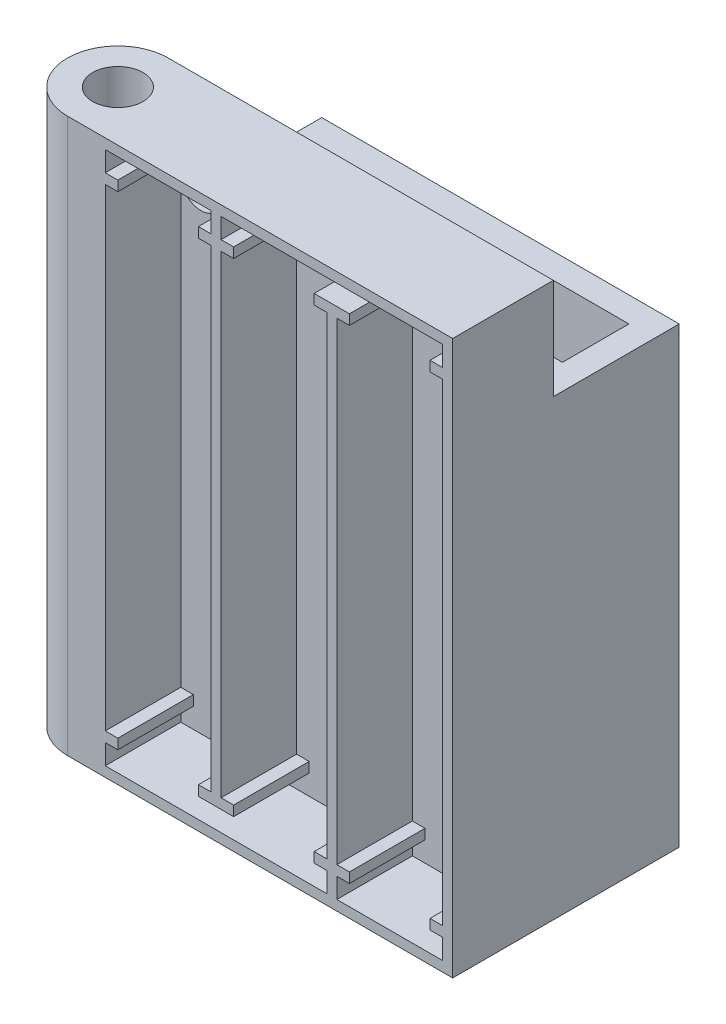
SolidWorks part; units mm, degrees
ref_plane "Front Plane" through (0, 0, 0) normal (0, 0, 1) x (1, 0, 0)
ref_plane "Top Plane" through (0, 0, 0) normal (0, 1, 0) x (1, 0, 0)
ref_plane "Right Plane" through (0, 0, 0) normal (1, 0, 0) x (0, 0, -1)
sketch "Sketch1" plane through (0, 0, 0) normal (0, 1, 0) x (1, 0, 0)
  line L1 (-15.25, -5) -> (15.25, -5)
  line L2 (-15.25, -5) -> (-15.25, 5)
  line L3 (-15.25, 5) -> (15.25, 5)
  line L4 (15.25, -5) -> (15.25, 5)
  line L5 (-15.25, -5) -> (15.25, 5) construction
  line L6 (-15.25, 5) -> (15.25, -5) construction
  point P0 (0, 0)
  dimension "D1" = 30.5
  dimension "D2" = 10
extrude "Boss-Extrude1" add sketch "Sketch1" along normal blind 2.5
sketch "Sketch2" plane through (0, 0, 0) normal (0, 1, 0) x (1, 0, 0)
  line L0 (15.25, 5) -> (-15.25, 5) construction
  line L1 (-17.75, -7.5) -> (17.75, -7.5)
  line L2 (-17.75, -7.5) -> (-17.75, 7.5)
  line L3 (-17.75, 7.5) -> (17.75, 7.5)
  line L4 (17.75, -7.5) -> (17.75, 7.5)
  line L5 (-17.75, -7.5) -> (17.75, 7.5) construction
  line L6 (-17.75, 7.5) -> (17.75, -7.5) construction
  line L7 (-15.25, 5) -> (-15.25, -5) construction
  line L8 (-15.25, 5) -> (-15.25, -5)
  line L9 (-15.25, -5) -> (-10.25, -5)
  line L10 (-15.25, -5) -> (15.25, -5) construction
  line L11 (-10.25, -5) -> (-10.25, -1.6)
  line L12 (-10.25, -1.6) -> (15.25, -1.6)
  line L13 (15.25, -5) -> (15.25, 5) construction
  line L14 (15.25, -1.6) -> (15.25, 5)
  line L15 (15.25, 5) -> (-15.25, 5)
  point P0 (0, 0)
  dimension "D1" = 2.5
  dimension "D2" = 2.5
  dimension "D3" = 6.6
  dimension "D4" = 5
extrude "Boss-Extrude3" add sketch "Sketch2" along normal blind 45
sketch "Sketch3" plane through (0, 45, 0) normal (0, 1, 0) x (1, 0, 0)
  line L0 (-10.25, -5) -> (-2.75, -5)
  line L1 (-2.75, -5) -> (-2.75, -1.6)
  line L2 (-10.25, -1.6) -> (15.25, -1.6) construction
  line L3 (-2.75, -1.6) -> (-10.25, -1.6)
  line L4 (-10.25, -1.6) -> (-10.25, -5)
  dimension "D1" = 7.5
extrude "Cut-Extrude1" cut sketch "Sketch3" against normal blind 29
sketch "Sketch4" plane through (0, 45, 0) normal (0, 1, 0) x (1, 0, 0)
  line L0 (-15.25, -5) -> (-17.75, -5) construction
  line L1 (-17.75, 7.5) -> (-17.75, -7.5) construction
  line L3 (17.75, -7.5) -> (-17.75, -7.5)
  line L4 (17.75, -7.5) -> (17.75, -5)
  line L5 (17.75, -5) -> (-17.75, -5)
  line L6 (-17.75, -7.5) -> (-17.75, -5)
extrude "Boss-Extrude4" add sketch "Sketch4" along normal blind 10
sketch "Sketch5" plane through (0, 0, 7.5) normal (0, 0, 1) x (1, 0, 0)
  line L5 (-17.75, 27.5) -> (17.75, 27.5) construction
  line L11 (-17.75, 55) -> (-17.75, 0) construction
  line L20 (17.75, 55) -> (17.75, 0) construction
  line L21 (-17.75, 0) -> (-17.75, 55)
  line L22 (-17.75, 55) -> (17.75, 55)
  line L23 (17.75, 55) -> (17.75, 0)
  line L24 (-16.75, 1) -> (-16.75, 54)
  line L25 (-16.75, 54) -> (16.75, 54)
  line L26 (16.75, 54) -> (16.75, 1)
  line L27 (-17.75, 0) -> (17.75, 0)
  line L28 (-16.75, 1) -> (16.75, 1)
  point P16 (16.75, 27.5)
  point P17 (-16.75, 27.5)
  dimension "D1" = 1
  dimension "D2" = 1
  dimension "D3" = 1
extrude "Boss-Extrude5" add sketch "Sketch5" along normal blind 7.5
sketch "Sketch6" plane through (0, 0, 7.5) normal (0, 0, 1) x (1, 0, 0)
  line L0 (-6.25, 54) -> (-6.25, 52)
  line L1 (16.75, 54) -> (-16.75, 54) construction
  line L2 (-16.75, 1) -> (16.75, 1) construction
  line L3 (-6.25, 1) -> (-5.25, 1)
  line L4 (-5.25, 1) -> (-5.25, 3)
  line L5 (-5.25, 54) -> (-6.25, 54)
  line L6 (-16.75, 54) -> (-16.75, 1) construction
  line L7 (6.25, 54) -> (5.25, 54)
  line L8 (5.25, 54) -> (5.25, 52)
  line L9 (5.25, 1) -> (6.25, 1)
  line L10 (6.25, 1) -> (6.25, 3)
  line L13 (16.75, 1) -> (16.75, 54) construction
  line L14 (-16.75, 52) -> (-6.25, 52)
  line L15 (-16.75, 52) -> (-16.75, 51)
  line L16 (-16.75, 51) -> (-6.25, 51)
  line L17 (16.75, 52) -> (16.75, 51)
  line L18 (16.75, 54) -> (-16.75, 54) construction
  line L19 (-16.75, 27.5) -> (16.75, 27.5) construction
  line L20 (-16.75, 54) -> (-16.75, 1) construction
  line L21 (-16.75, 4) -> (-6.25, 4)
  line L22 (16.75, 3) -> (16.75, 4)
  line L23 (-16.75, 3) -> (-6.25, 3)
  line L24 (-16.75, 3) -> (-16.75, 4)
  line L25 (-6.25, 51) -> (-6.25, 4)
  line L26 (-5.25, 52) -> (-5.25, 54)
  line L27 (-5.25, 52) -> (5.25, 52)
  line L28 (-5.25, 51) -> (5.25, 51)
  line L29 (6.25, 52) -> (6.25, 54)
  line L30 (5.25, 51) -> (5.25, 4)
  line L31 (6.25, 52) -> (16.75, 52)
  line L32 (6.25, 51) -> (16.75, 51)
  line L33 (-5.25, 3) -> (5.25, 3)
  line L34 (-5.25, 4) -> (5.25, 4)
  line L35 (-6.25, 3) -> (-6.25, 1)
  line L36 (-5.25, 4) -> (-5.25, 51)
  line L37 (6.25, 3) -> (16.75, 3)
  line L38 (6.25, 4) -> (16.75, 4)
  line L39 (5.25, 3) -> (5.25, 1)
  line L40 (6.25, 4) -> (6.25, 51)
  dimension "D1" = 1
  dimension "D2" = 10.5
  dimension "D4" = 10.5
  dimension "D5" = 1
  dimension "D6" = 2
  dimension "D3" = 2
extrude "Boss-Extrude6" add sketch "Sketch6" along normal blind 7.5
sketch "Sketch7" plane through (0, 0, 15) normal (0, 0, 1) x (1, 0, 0)
  line L0 (-16.75, 27.5) -> (16.75, 27.5) construction
  line L1 (-16.75, 51) -> (-16.75, 4) construction
  line L2 (16.75, 4) -> (16.75, 51) construction
  line L3 (-11.5, 52) -> (-11.5, 51) construction
  line L6 (-6.25, 52) -> (-16.75, 52) construction
  line L9 (-16.75, 51) -> (-6.25, 51) construction
  line L12 (-4, 51) -> (-4, 52)
  line L13 (-15.5, 51) -> (-7.5, 51)
  line L14 (-15.5, 51) -> (-15.5, 52)
  line L15 (-15.5, 52) -> (-7.5, 52)
  line L16 (-7.5, 51) -> (-7.5, 52)
  line L17 (-15.5, 51) -> (-7.5, 52) construction
  line L18 (-15.5, 52) -> (-7.5, 51) construction
  line L19 (-4, 51) -> (4, 51)
  line L20 (4, 51) -> (4, 52)
  line L21 (-4, 52) -> (4, 52)
  line L22 (7.5, 51) -> (7.5, 52)
  line L23 (7.5, 51) -> (15.5, 51)
  line L24 (15.5, 51) -> (15.5, 52)
  line L25 (7.5, 52) -> (15.5, 52)
  line L28 (7.5, 4) -> (15.5, 4)
  line L29 (5.25, 54) -> (6.25, 54)
  line L30 (5.25, 54) -> (5.25, 52)
  line L31 (5.25, 52) -> (6.25, 52)
  line L32 (6.25, 54) -> (6.25, 52)
  line L33 (15.5, 4) -> (15.5, 3)
  line L34 (7.5, 3) -> (15.5, 3)
  line L35 (7.5, 4) -> (7.5, 3)
  line L36 (-4, 4) -> (4, 4)
  line L37 (4, 4) -> (4, 3)
  line L38 (-4, 3) -> (4, 3)
  line L39 (-4, 4) -> (-4, 3)
  line L40 (-15.5, 3) -> (-7.5, 3)
  line L41 (-7.5, 4) -> (-7.5, 3)
  line L42 (-15.5, 4) -> (-7.5, 4)
  line L43 (-15.5, 4) -> (-15.5, 3)
  line L45 (-6.25, 3) -> (-5.25, 3)
  line L46 (-6.25, 3) -> (-6.25, 1)
  line L47 (-6.25, 1) -> (-5.25, 1)
  line L48 (-5.25, 3) -> (-5.25, 1)
  point P12 (-11.5, 51.5)
  dimension "D1" = 8
  dimension "D3" = 3.5
  dimension "D2" = 3
extrude "Cut-Extrude2" cut sketch "Sketch7" against normal up to surface (7.5 mm away) up to face at (0, 27.5, 7.5)
sketch "Sketch8" plane through (0, 0, 7.5) normal (0, 0, 1) x (1, 0, 0)
  line L0 (11.5, 1) -> (11.5, 54) construction
  line L3 (6.25, 1) -> (16.75, 1) construction
  line L8 (16.75, 54) -> (-5.25, 54) construction
  line L9 (-11.5, 54) -> (-11.5, 1) construction
  line L10 (10.7, 47) -> (12.3, 47)
  line L11 (10.7, 47) -> (10.7, 1)
  line L12 (10.7, 1) -> (12.3, 1)
  line L13 (12.3, 47) -> (12.3, 1)
  line L14 (10.7, 47) -> (12.3, 1) construction
  line L15 (10.7, 1) -> (12.3, 47) construction
  line L16 (-6.25, 54) -> (-16.75, 54) construction
  line L17 (-16.75, 1) -> (5.25, 1) construction
  line L18 (-6.25, 54) -> (-16.75, 54) construction
  line L19 (-12.3, 45) -> (-10.7, 45)
  line L20 (-12.3, 45) -> (-12.3, 54)
  line L21 (-12.3, 54) -> (-10.7, 54)
  line L22 (-10.7, 45) -> (-10.7, 54)
  line L23 (-12.3, 45) -> (-10.7, 54) construction
  line L24 (-12.3, 54) -> (-10.7, 45) construction
  point P6 (11.5, 24)
  point P17 (-11.5, 49.5)
  dimension "D1" = 1.6
  dimension "D2" = 7
  dimension "D3" = 1.6
  dimension "D4" = 9
extrude "Cut-Extrude3" cut sketch "Sketch8" against normal blind 2.5
sketch "Sketch9" plane through (0, 0, 7.5) normal (0, 0, 1) x (1, 0, 0)
  line L0 (-12.3, 45) -> (-16.75, 45) construction
  line L1 (-16.75, 51) -> (-16.75, 4) construction
  line L2 (0, 0) -> (0, 54) construction
  line L3 (16.75, 54) -> (-5.25, 54) construction
  line L4 (-14.75, 45) -> (-14.75, 51) construction
  line L7 (-16.75, 51) -> (-15.5, 51) construction
  line L8 (-17.75, 55) -> (-17.75, 0) construction
  circle A0 centre (-14.75, 48) radius 1
  circle A1 centre (14.75, 48) radius 1
  dimension "D1" = 2
  dimension "D2" = 3
extrude "Cut-Extrude4" cut sketch "Sketch9" against normal up to next
sketch "Sketch10" plane through (0, 0, 7.5) normal (0, 0, 1) x (1, 0, 0)
  line L0 (0, 0) -> (0, 55) construction
  line L1 (17.75, 55) -> (-17.75, 55) construction
  circle A0 centre (-14.75, 48) radius 2
  circle A1 centre (14.75, 48) radius 2
  dimension "D1" = 4
extrude "Cut-Extrude5" cut sketch "Sketch10" against normal blind 1
sketch "Sketch11" plane through (0, 55, 0) normal (0, 1, 0) x (1, 0, 0)
  line L0 (-17.75, -5) -> (-20.5, -5)
  line L5 (-17.75, -15) -> (-20.5, -15)
  line L6 (-17.75, -5) -> (-17.75, -15)
  arc A2 (-20.5, -5) -> (-20.5, -15) centre (-20.5, -10) ccw
  circle A3 centre (-20.5, -10) radius 2.5
  dimension "D3" = 5
  dimension "D1" = 2.75
  dimension "D2" = 2.75
extrude "Boss-Extrude8" add sketch "Sketch11" against normal up to surface (55 mm away) up to face at (0, 0, 3.75)
